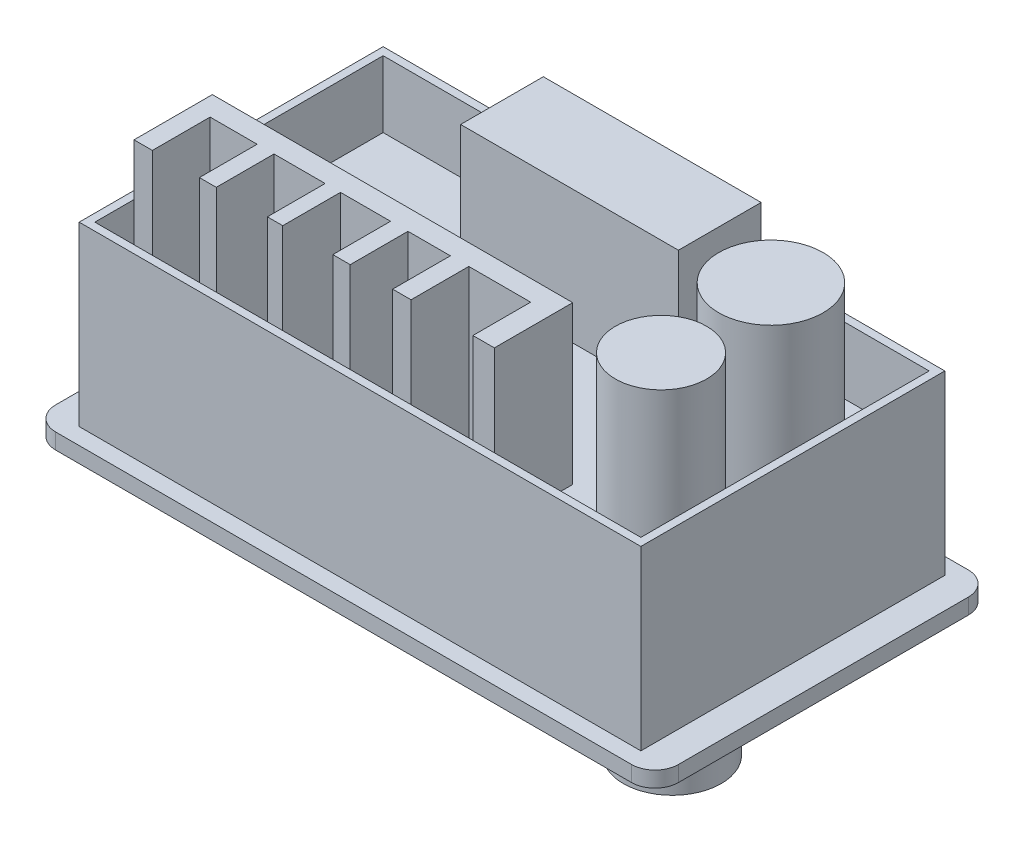
SolidWorks part; units mm, degrees
ref_plane "Front Plane" through (0, 0, 0) normal (0, 0, 1) x (1, 0, 0)
ref_plane "Top Plane" through (0, 0, 0) normal (0, 1, 0) x (1, 0, 0)
ref_plane "Right Plane" through (0, 0, 0) normal (1, 0, 0) x (0, 0, -1)
sketch "Sketch1" plane through (0, 0, 0) normal (0, 1, 0) x (1, 0, 0)
  line L1 (-14.6751, 3.6977) -> (64.8249, 3.6977)
  line L2 (-14.6751, 3.6977) -> (-14.6751, -39.3023)
  line L3 (-14.6751, -39.3023) -> (64.8249, -39.3023)
  line L4 (64.8249, 3.6977) -> (64.8249, -39.3023)
  dimension "D1" = 43
  dimension "D2" = 79.5
extrude "Boss-Extrude1" add sketch "Sketch1" along normal blind 2
sketch "Sketch2" plane through (0, 2, 0) normal (0, 1, 0) x (1, 0, 0)
  line L0 (64.8249, -39.3023) -> (64.8249, 3.6977) construction
  line L1 (-10.7751, 1.5977) -> (60.9249, 1.5977)
  line L2 (-10.7751, 1.5977) -> (-10.7751, -37.2023)
  line L3 (-10.7751, -37.2023) -> (60.9249, -37.2023)
  line L4 (60.9249, 1.5977) -> (60.9249, -37.2023)
  line L5 (-14.6751, 3.6977) -> (-14.6751, -39.3023) construction
  line L6 (-14.6751, -39.3023) -> (64.8249, -39.3023) construction
  line L7 (64.8249, 3.6977) -> (-14.6751, 3.6977) construction
  dimension "D1" = 3.9
  dimension "D2" = 3.9
  dimension "D3" = 2.1
  dimension "D4" = 2.1
extrude "Boss-Extrude2" add sketch "Sketch2" along normal blind 22.6
sketch "Sketch3" plane through (0, 24.6, 0) normal (0, 1, 0) x (1, 0, 0)
  line L0 (60.9249, -37.2023) -> (60.9249, 1.5977) construction
  line L1 (-9.7751, 0.5977) -> (59.9249, 0.5977)
  line L2 (-9.7751, 0.5977) -> (-9.7751, -36.2023)
  line L3 (-9.7751, -36.2023) -> (59.9249, -36.2023)
  line L4 (59.9249, 0.5977) -> (59.9249, -36.2023)
  line L5 (-10.7751, -37.2023) -> (60.9249, -37.2023) construction
  line L6 (-10.7751, 1.5977) -> (-10.7751, -37.2023) construction
  line L7 (60.9249, 1.5977) -> (-10.7751, 1.5977) construction
  dimension "D1" = 1
  dimension "D2" = 1
  dimension "D3" = 1
  dimension "D4" = 1
extrude "Cut-Extrude1" cut sketch "Sketch3" against normal blind 8.5
sketch "Sketch5" plane through (0, 16.1, 0) normal (0, 1, 0) x (1, 0, 0)
  line L0 (-9.7751, -36.2023) -> (59.9249, -36.2023) construction
  line L1 (-4.7751, -26.2023) -> (41.2249, -26.2023)
  line L2 (-4.7751, -26.2023) -> (-4.7751, -36.2023)
  line L3 (-4.7751, -36.2023) -> (41.2249, -36.2023)
  line L4 (41.2249, -26.2023) -> (41.2249, -36.2023)
  line L5 (-9.7751, 0.5977) -> (-9.7751, -36.2023) construction
  line L7 (-2.433, -28.8316) -> (3.5711, -28.8316)
  line L8 (-2.433, -28.8316) -> (-2.433, -36.2023)
  line L9 (-2.433, -36.2023) -> (3.5711, -36.2023)
  line L10 (3.5711, -28.8316) -> (3.5711, -36.2023)
  line L11 (5.7247, -28.8316) -> (12.2509, -28.8316)
  line L12 (5.7247, -28.8316) -> (5.7247, -36.2023)
  line L13 (5.7247, -36.2023) -> (12.2509, -36.2023)
  line L14 (12.2509, -28.8316) -> (12.2509, -36.2023)
  line L15 (14.2088, -28.8316) -> (20.6044, -28.8316)
  line L16 (14.2088, -28.8316) -> (14.2088, -36.2023)
  line L17 (14.2088, -36.2023) -> (20.6044, -36.2023)
  line L18 (20.6044, -28.8316) -> (20.6044, -36.2023)
  line L19 (22.8233, -28.8316) -> (28.2401, -28.8316)
  line L20 (22.8233, -28.8316) -> (22.8233, -36.2023)
  line L21 (22.8233, -36.2023) -> (28.2401, -36.2023)
  line L22 (28.2401, -28.8316) -> (28.2401, -36.2023)
  line L23 (30.5895, -28.8316) -> (38.4862, -28.8316)
  line L24 (30.5895, -28.8316) -> (30.5895, -36.2023)
  line L25 (30.5895, -36.2023) -> (38.4862, -36.2023)
  line L26 (38.4862, -28.8316) -> (38.4862, -36.2023)
  line M10 (-9.7751, -36.2023) -> (59.9249, -36.2023)
  dimension "D1" = 46
  dimension "D2" = 10
  dimension "D3" = 5
extrude "Boss-Extrude3" add sketch "Sketch5" along normal blind 22.6 contours L23 L26 L4 L1 L2 L8 L7 L10 L12 L11 L14 L16 L15 L18 L20 L19 L22 L24 M10
sketch "Sketch6" plane through (0, 0, 37.2023) normal (0, 0, 1) x (1, 0, 0)
  line L0 (-10.7751, 24.6) -> (60.9249, 24.6) construction
  line L1 (-14.637, 45.1409) -> (52.5827, 45.1409)
  line L2 (-14.637, 45.1409) -> (-14.637, 36.2)
  line L3 (-14.637, 36.2) -> (52.5827, 36.2)
  line L4 (52.5827, 45.1409) -> (52.5827, 36.2)
  dimension "D1" = 11.6
extrude "Cut-Extrude2" cut sketch "Sketch6" against normal blind 22.6
sketch "Sketch7" plane through (0, 16.1, 0) normal (0, 1, 0) x (1, 0, 0)
  circle A0 centre (51.669, -11.3414) radius 6.6637
  circle A1 centre (52.3869, -26.0906) radius 5.8292
extrude "Boss-Extrude4" add sketch "Sketch7" along normal up to surface (20.1 mm away) up to face at (17.543, 36.2, 32.2978)
fillet "Fillet1" radius 3 4 edges at (-14.6751, 1, -3.6977) (64.8249, 1, -3.6977) (64.8249, 1, 39.3023) (-14.6751, 1, 39.3023)
sketch "Sketch8" plane through (0, 16.1, 0) normal (0, 1, 0) x (1, 0, 0)
  line L1 (11.272, 0) -> (39.0735, 0)
  line L2 (11.272, 0) -> (11.272, -10.5583)
  line L3 (11.272, -10.5583) -> (39.0735, -10.5583)
  line L4 (39.0735, 0) -> (39.0735, -10.5583)
extrude "Boss-Extrude5" add sketch "Sketch8" along normal blind 17
sketch "Sketch9" plane through (0, 0, 0) normal (0, -1, 0) x (1, 0, 0)
  line L0 (64.8249, 36.3023) -> (64.8249, -0.6977) construction
  line L1 (-8.6751, 33.3023) -> (58.8249, 33.3023)
  line L2 (-8.6751, 33.3023) -> (-8.6751, 2.3023)
  line L3 (-8.6751, 2.3023) -> (58.8249, 2.3023)
  line L4 (58.8249, 33.3023) -> (58.8249, 2.3023)
  line L5 (61.8249, -3.6977) -> (-11.6751, -3.6977) construction
  line L6 (-14.6751, -0.6977) -> (-14.6751, 36.3023) construction
  line L7 (-11.6751, 39.3023) -> (61.8249, 39.3023) construction
  dimension "D1" = 6
  dimension "D2" = 6
  dimension "D3" = 6
  dimension "D4" = 6
extrude "Cut-Extrude3" cut sketch "Sketch9" against normal blind 1
sketch "Sketch10" plane through (0, 1, 0) normal (0, -1, 0) x (1, 0, 0)
  line L1 (4.1584, 30.5936) -> (33.0042, 30.5936)
  line L2 (4.1584, 30.5936) -> (4.1584, 4.6194)
  line L3 (4.1584, 4.6194) -> (33.0042, 4.6194)
  line L4 (33.0042, 30.5936) -> (33.0042, 4.6194)
extrude "Cut-Extrude4" cut sketch "Sketch10" against normal blind 1
sketch "Sketch11" plane through (0, 1, 0) normal (0, -1, 0) x (1, 0, 0)
  circle A0 centre (50.4291, 22.697) radius 6.25
  dimension "D1" = 12.5
extrude "Boss-Extrude6" add sketch "Sketch11" along normal blind 12 contours A0
